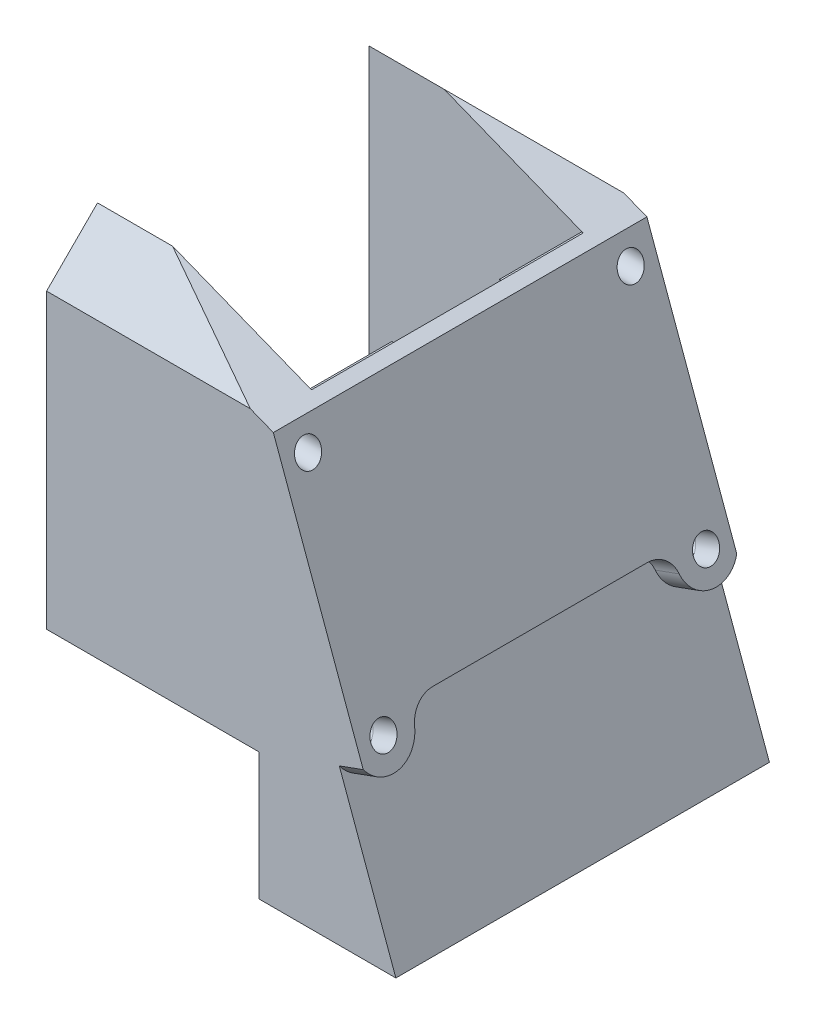
SolidWorks part; units mm, degrees
ref_plane "Front Plane" through (0, 0, 0) normal (0, 0, 1) x (1, 0, 0)
ref_plane "Top Plane" through (0, 0, 0) normal (0, 1, 0) x (1, 0, 0)
ref_plane "Right Plane" through (0, 0, 0) normal (1, 0, 0) x (0, 0, -1)
sketch "Sketch1" plane through (0, 0, 0) normal (0, 0, 1) x (1, 0, 0)
  line L0 (-25, 22) -> (1.7101, 11.4259)
  line L1 (0, 16.1243) -> (54.7232, -134.2265) construction
  line L2 (1.7101, 11.4259) -> (19.3357, -37)
  line L3 (19.3357, -37) -> (2.5, -37)
  line L4 (2.5, -55.7) -> (2.5, -23) construction
  line L5 (2.5, -37) -> (2.5, -22)
  line L6 (2.5, -22) -> (-25, -22)
  line L7 (-25, -22) -> (-25, 22)
  dimension "D1" = 15
  dimension "D2" = 5
extrude "Boss-Extrude1" add sketch "Sketch1" along normal up to surface (6 mm away)
sketch "Sketch2" plane through (-25, 0, 0) normal (-1, 0, 0) x (0, 0, 1)
  line L0 (6, 12.5) -> (-3.5, 22) construction
  line L1 (0, 22) -> (0, -22) construction
  line L2 (6, 22) -> (0, 22) construction
  line L3 (6, -22) -> (6, 22) construction
  line L4 (6, 12.5) -> (-3.5, 22)
  line L5 (0, 22) -> (0, -22)
  line L6 (6, 22) -> (0, 22)
  line L7 (6, -22) -> (6, 22)
  line M2 (6, -22) -> (6, 22)
  line M3 (6, 22) -> (0, 22)
  line M4 (0, 22) -> (0, -22)
extrude "Cut-Extrude1" cut sketch "Sketch2" against normal through all contours L4 M2 M3 M4
sketch "Sketch3" plane through (0, 0, 0) normal (0, 0, -1) x (-1, 0, 0)
  line L0 (-19.3357, -37) -> (-1.7101, 11.4259) construction
  line L1 (-1.7101, 11.4259) -> (16.159, 18.5) construction
  line L2 (-0.2, 14.65) -> (-0.2, 1.35) construction
  line L3 (0, -23) -> (0, 18) construction
  line L4 (25, -22) -> (-2.5, -22) construction
  line L5 (-2.5, -22) -> (-2.5, -37) construction
  line L6 (-2.5, -37) -> (-19.3357, -37) construction
  line L7 (-19.3357, -37) -> (-1.7101, 11.4259)
  line L8 (-1.7101, 11.4259) -> (16.159, 18.5)
  line L9 (-0.2, 14.65) -> (-0.2, 1.35)
  line L10 (0, -23) -> (0, 18)
  line L11 (25, -22) -> (-2.5, -22)
  line L12 (-2.5, -22) -> (-2.5, -37)
  line L13 (-2.5, -37) -> (-19.3357, -37)
  line L14 (-0.2, 1.35) -> (0, 1.35)
  line M3 (-1.7101, 11.4259) -> (-19.3357, -37)
  line M4 (-19.3357, -37) -> (-2.5, -37)
  line M5 (-2.5, -37) -> (-2.5, -22)
  line M6 (-2.5, -22) -> (25, -22)
extrude "Boss-Extrude2" add sketch "Sketch3" along normal up to surface (32 mm away) contours L14 L9 L8 L10 M3 M4 M5 M6
sketch "Sketch4" plane through (0.2, 0, 0) normal (-1, 0, 0) x (0, 0, 1)
  line L0 (-32, 1.35) -> (0, 1.35) construction
  line L1 (0, 18.5) -> (0, -22) construction
  line L2 (-32, 12.0237) -> (0, 12.0237) construction
  line L3 (-32, 1.35) -> (-32, 12.0237) construction
  line L4 (-32, 1.35) -> (0, 1.35)
  line L5 (0, 18.5) -> (0, -22)
  line L6 (-32, 12.0237) -> (0, 12.0237)
  line L7 (-32, 1.35) -> (-32, 12.0237)
  circle A0 centre (-16, 8) radius 7.5
  line M1 (-32, 12.0237) -> (-32, 1.35)
  line M2 (-32, 1.35) -> (0, 1.35)
  line M3 (0, 1.35) -> (0, 12.0237)
  line M4 (0, 12.0237) -> (-32, 12.0237)
  dimension "D1" = 15
extrude "Boss-Extrude3" add sketch "Sketch4" along normal up to surface (0.2 mm away) contours A0 M4 M1 M2 | A0 M2 M3 M4 up to face at (0, -13.2437, -20)
sketch "Sketch5" plane through (0, -22, 0) normal (0, -1, 0) x (1, 0, 0)
  line L0 (0, -32) -> (0, 0) construction
  line L1 (0, -32) -> (0, 0)
  line L2 (0, 0) -> (0, 6)
  line L3 (2.5, 6) -> (-25, 6) construction
  line L4 (0, 6) -> (2.5, 6)
  line L5 (2.5, 6) -> (2.5, -32)
  line L6 (2.5, -32) -> (0, -32)
  arc A0 (-11.6056, -25.8586) -> (-21.8586, -15.6056) centre (-9.75, -13.75) ccw construction
  arc A1 (-11.6056, -25.8586) -> (-21.8586, -15.6056) centre (-9.75, -13.75) ccw
  line M1 (2.5, -32) -> (2.5, 6)
  line M2 (2.5, 6) -> (-25, 6)
  line M5 (0, 0) -> (0, -32)
  line M6 (0, -32) -> (2.5, -32)
extrude "Boss-Extrude4" add sketch "Sketch5" along normal up to surface (15 mm away) contours A1 L5 L2 M2 M5 | A1 M5 M6 M1 up to face at (10.9178, -37, -13)
sketch "Sketch6" plane through (0, 0, -32) normal (0, 0, -1) x (-1, 0, 0)
  line L6 (25, 22) -> (-1.7101, 11.4259)
  line L7 (-1.7101, 11.4259) -> (-19.3357, -37)
  line L8 (-19.3357, -37) -> (-2.5, -37)
  line L9 (-2.5, -37) -> (-2.5, -22)
  line L10 (-2.5, -22) -> (25, -22)
  line L11 (25, -22) -> (25, 22)
  line L12 (25, 22) -> (-1.7101, 11.4259)
  line L13 (-1.7101, 11.4259) -> (-19.3357, -37)
  line L14 (-19.3357, -37) -> (-2.5, -37)
  line L15 (-2.5, -37) -> (-2.5, -22)
  line L16 (-2.5, -22) -> (25, -22)
  line L17 (25, -22) -> (25, 22)
  dimension "D1" = 0
extrude "Boss-Extrude5" add sketch "Sketch6" along normal up to surface (6 mm away)
sketch "Sketch7" plane through (-25, 0, 0) normal (-1, 0, 0) x (0, 0, 1)
  line L0 (-38, 22) -> (-32, 22)
  line L1 (-32, 22) -> (-32, 18.5)
  line L2 (-32, -22) -> (-32, 22) construction
  line L3 (-32, 18.5) -> (-38, 12.5)
  line L4 (-38, 22) -> (-38, -22) construction
  line L5 (-28.5, 22) -> (-38, 12.5) construction
  line L6 (-38, 12.5) -> (-38, 22)
extrude "Cut-Extrude2" cut sketch "Sketch7" against normal through all
sketch "Sketch8" plane through (-25, 0, 0) normal (-1, 0, 0) x (0, 0, 1)
  circle A0 centre (-35, 8.4289) radius 1.5 construction
  circle A1 centre (-35, -17) radius 1.5 construction
  circle A2 centre (3, -17) radius 1.5 construction
  circle A3 centre (3, 8.4289) radius 1.5 construction
  circle A4 centre (-35, 8.4289) radius 1.5
  circle A5 centre (-35, -17) radius 1.5
  circle A6 centre (3, -17) radius 1.5
  circle A7 centre (3, 8.4289) radius 1.5
extrude "Cut-Extrude3" cut sketch "Sketch8" against normal through all
sketch "Sketch9" plane through (0, -37, 0) normal (0, -1, 0) x (1, 0, 0)
  line L0 (-25, -38) -> (2.5, -38) construction
  line L1 (2.5, -32) -> (0, -32)
  line L2 (2.5, -32) -> (2.5, -38)
  line L3 (2.5, -38) -> (0, -38)
  line L4 (0, -32) -> (0, -38)
  line L5 (0, -32) -> (-25, -32) construction
  line L6 (0, -32) -> (0, -21.1662) construction
extrude "Boss-Extrude6" add sketch "Sketch9" against normal up to surface (15 mm away) up to face at (-9, -22, -34.4)
sketch "Sketch10" plane through (5.1823, 1.8862, 0) normal (0.9397, 0.342, 0) x (0, 0, -1)
  line L0 (38, -41.3818) -> (38, -17.3818)
  line L1 (38, -41.3818) -> (38, 10.1519) construction
  line L2 (38, -17.3818) -> (-6, -17.3818)
  line L3 (-6, 10.1519) -> (-6, -41.3818) construction
  line L4 (-6, -17.3818) -> (-6, -41.3818)
  line L5 (-6, -41.3818) -> (38, -41.3818)
  dimension "D1" = 24
extrude "Cut-Extrude4" cut sketch "Sketch10" against normal blind 3
sketch "Sketch11" plane through (2.3632, 0.8601, 0) normal (0.9397, 0.342, 0) x (0, 0, -1)
  line L0 (38, -17.3818) -> (-6, -17.3818) construction
  line L1 (-6, -17.3818) -> (-6, -40.2899) construction
  line L2 (38, -40.2899) -> (38, -17.3818) construction
  line L3 (38, -17.3818) -> (-6, -17.3818)
  line L4 (-6, -17.3818) -> (-6, -40.2899)
  line L5 (38, -40.2899) -> (38, -17.3818)
  circle A0 centre (-3, -19.0064) radius 3.5
  circle A1 centre (35, -19.0064) radius 3.5
  ellipse M1 centre (35, -19.0064) end of major axis (35, -17.4101) minor radius 1.5
  ellipse M2 centre (-3, -19.0064) end of major axis (-3, -17.4101) minor radius 1.5
  line M5 (38, -17.3818) -> (-6, -17.3818)
  line M6 (-6, -17.3818) -> (-6, -40.2899)
  dimension "D1" = 7
extrude "Boss-Extrude7" add sketch "Sketch11" along normal up to surface (3 mm away) contours A0 L3 M6 M2 | A1 L5 M5 M1 up to face at (2.2549, 9.9289, 3)
fillet "Fillet1" radius 3 2 edges at (9.7177, -14.9604, -31.8999) (9.7177, -14.9604, -0.1001)
